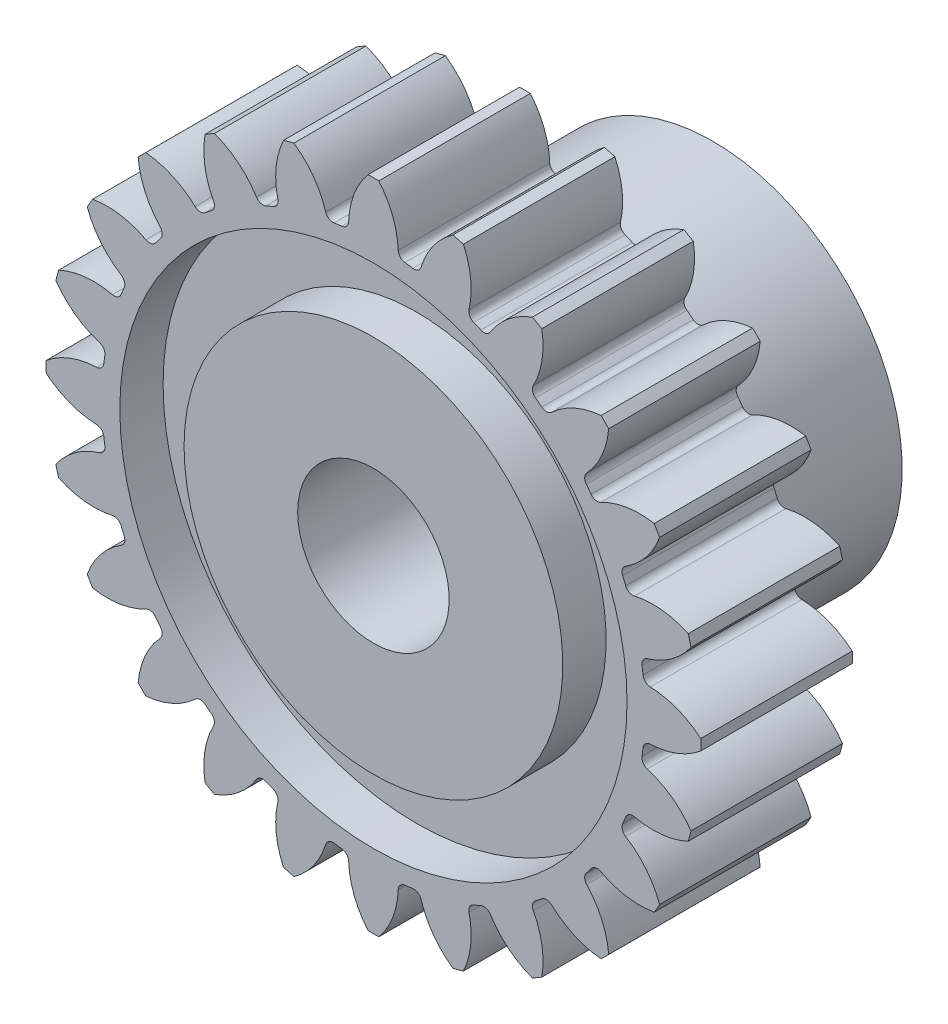
SolidWorks part; units mm, degrees
ref_plane "Front Plane" through (0, 0, 0) normal (0, 0, 1) x (1, 0, 0)
ref_plane "Top Plane" through (0, 0, 0) normal (0, 1, 0) x (1, 0, 0)
ref_plane "Right Plane" through (0, 0, 0) normal (1, 0, 0) x (0, 0, -1)
sketch "Sketch1" plane through (0, 0, 0) normal (1, 0, 0) x (0, 0, -1)
  line L0 (-7.112, 0) -> (-7.112, 13.7223)
  line L1 (-7.112, 13.7223) -> (-0.762, 13.7223)
  line L2 (-0.762, 13.7223) -> (-0.762, 7.9375)
  line L3 (-0.762, 7.9375) -> (7.112, 7.9375)
  line L4 (7.112, 7.9375) -> (7.112, 0)
  line L5 (7.112, 0) -> (-7.112, 0) construction
  line L6 (-7.112, 3.175) -> (7.112, 3.175)
  point P9 (-7.112, 10.6299)
  dimension "OD" = 27.4447
  dimension "Face Width" = 6.35
  dimension "Hub Width" = 7.874
  dimension "Hub Diameter" = 15.875
  dimension "For Shaft Diameter" = 6.35
  dimension "Overall Width" = 14.224
  dimension "Under Cut Diameter" = 21.2598
sketch "Sketch2" plane through (0, 0, 0) normal (0, 0, 1) x (1, 0, 0)
  line L0 (-1.3313, 11.2989) -> (-0.4492, 13.7223)
  line L1 (-0.4492, 13.7223) -> (0.4492, 13.7223)
  line L2 (0.4492, 13.7223) -> (1.3313, 11.2989)
  line L3 (0, 13.7223) -> (0, 0) construction
  line L4 (0, 0) -> (-1.7911, 13.605) construction
  line L5 (0, 0) -> (1.7911, 13.605) construction
  line L6 (-4.2103, 10.5694) -> (-3.9855, 13.1385)
  line L7 (-3.9855, 13.1385) -> (-3.1177, 13.371)
  line L8 (-3.1177, 13.371) -> (-1.6385, 11.2585)
  line L9 (-3.5516, 13.2548) -> (0, 0) construction
  line L11 (-0.4492, 13.7223) -> (0, 13.7223) construction
  line L12 (-0.8312, 12.6728) -> (0.8312, 12.6728) construction
  circle A0 centre (0, 0) radius 12.7 construction
  circle A2 centre (0, 0) radius 13.7223
  circle A3 centre (0, 0) radius 11.3771
  arc A5 (-0.2246, 13.7223) -> (-1.0378, 11.3296) centre (2.4404, 11.482) ccw
  arc A6 (1.0378, 11.3296) -> (0.2246, 13.7223) centre (-2.4404, 11.482) ccw
  arc A7 (-1.9298, 11.2122) -> (-3.3347, 13.3129) centre (-5.329, 10.4591) ccw
  arc A8 (-0.8312, 12.6728) -> (0.8312, 12.6728) centre (0, 0) cw
  point P3 (0, 12.7)
  point P5 (3.287, 12.2673)
  point P6 (-10.9985, 6.35)
  point P9 (6.35, 10.9985)
  point P10 (8.9803, 8.9803)
  point P11 (10.9985, 6.35)
  point P12 (12.2673, 3.287)
  point P13 (12.7, 0)
  point P14 (12.2673, -3.287)
  point P15 (10.9985, -6.35)
  point P16 (8.9803, -8.9803)
  point P17 (6.35, -10.9985)
  point P18 (3.287, -12.2673)
  point P19 (0, -12.7)
  point P20 (-3.287, -12.2673)
  point P21 (-6.35, -10.9985)
  point P22 (-8.9803, -8.9803)
  point P23 (-10.9985, -6.35)
  point P24 (-12.2673, -3.287)
  point P25 (-12.7, 0)
  point P26 (-12.2673, 3.287)
  point P27 (-8.9803, 8.9803)
  point P28 (-6.35, 10.9985)
  point P29 (-3.287, 12.2673)
  point P31 (0, 0)
  dimension "Gear Pitch Diameter" = 25.4
  dimension "Pressure Angle" = 20
  dimension "Addendum" = 1.0223
  dimension "Dedendum" = 1.3229
  dimension "D1" = 15
  dimension "D2" = 1.6624
  dimension "Number of Teeth" = 24
sketch "Sketch3" plane through (0, 0, 0) normal (1, 0, 0) x (0, 0, -1)
  line L0 (-7.112, 13.7223) -> (-0.762, 13.7223) construction
  line L1 (7.112, 7.9375) -> (7.112, 0) construction
  line L2 (-0.762, 7.9375) -> (7.112, 7.9375) construction
  line L3 (-0.762, 13.7223) -> (-0.762, 7.9375) construction
  line L4 (-7.112, 0) -> (-7.112, 13.7223) construction
  line L5 (-7.112, 3.175) -> (7.112, 3.175) construction
  line L6 (-7.112, 13.7223) -> (-0.762, 13.7223)
  line L7 (7.112, 7.9375) -> (7.112, 3.175)
  line L8 (-7.112, 7.9375) -> (-5.2977, 7.9375)
  line L9 (-0.762, 13.7223) -> (-0.762, 10.6299)
  line L10 (-7.112, 3.175) -> (-7.112, 7.9375)
  line L11 (-7.112, 3.175) -> (7.112, 3.175)
  line L12 (-7.112, 10.6299) -> (-5.2977, 10.6299)
  line L13 (-5.2977, 10.6299) -> (-5.2977, 7.9375)
  line L14 (-0.762, 10.6299) -> (-2.5763, 10.6299)
  line L15 (-2.5763, 10.6299) -> (-2.5763, 7.9375)
  line L16 (-2.5763, 7.9375) -> (7.112, 7.9375)
  line L17 (-7.112, 10.6299) -> (-7.112, 13.7223)
  dimension "D1" = 1.8143
revolve "Revolve1" add sketch "Sketch3" angle 360 about L5
sketch "Sketch4" plane through (0, 0, 7.112) normal (0, 0, 1) x (1, 0, 0)
  arc A1 (-0.2246, 13.7223) -> (-1.0378, 11.3296) centre (2.4404, 11.482) ccw construction
  arc A2 (-1.9298, 11.2122) -> (-3.3347, 13.3129) centre (-5.329, 10.4591) ccw construction
  arc A3 (-0.2262, 13.7205) -> (-1.039, 11.6045) centre (2.4404, 11.482) ccw
  arc A4 (-1.9998, 11.478) -> (-3.3327, 13.3115) centre (-5.329, 10.4591) ccw
  circle A5 centre (0, 0) radius 13.7223 construction
  arc A6 (-0.2262, 13.7205) -> (-3.3327, 13.3115) centre (0, 0) ccw
  circle A7 centre (0, 0) radius 11.3771 construction
  arc A8 (-1.3195, 11.3003) -> (-1.6502, 11.2568) centre (0, 0) ccw
  arc A9 (-1.9998, 11.478) -> (-1.6502, 11.2568) centre (-1.6962, 11.5709) ccw
  arc A10 (-1.3195, 11.3003) -> (-1.039, 11.6045) centre (-1.3563, 11.6157) ccw
  dimension "D1" = 0.3175
extrude "Cut-Extrude1" cut sketch "Sketch4" against normal through all both and the other way through all
pattern_circular "CirPattern1" count 24 over 360 about axis through (0, 0, 0) along (0, 0, 1) of "Cut-Extrude1"
equation "\"Dedendum@Sketch2\" = 1.25 /  ( \"Number of Teeth@Sketch2\" / \"Gear Pitch Diameter@Sketch2\" ) "
equation "\"D1@Sketch2\"=360/\"Number of Teeth@Sketch2\""
equation "\"D1@Sketch4\"=.3/(\"Number of Teeth@Sketch2\"/\"Gear Pitch Diameter@Sketch2\")"
equation "\"D1@CirPattern1\"=\"Number of Teeth@Sketch2\""
equation "\"D2@Sketch2\"=1.5708/(\"Number of Teeth@Sketch2\"/\"Gear Pitch Diameter@Sketch2\")"
equation "\"D1@Sketch3\"=\"Face Width@Sketch1\"/3.5"
